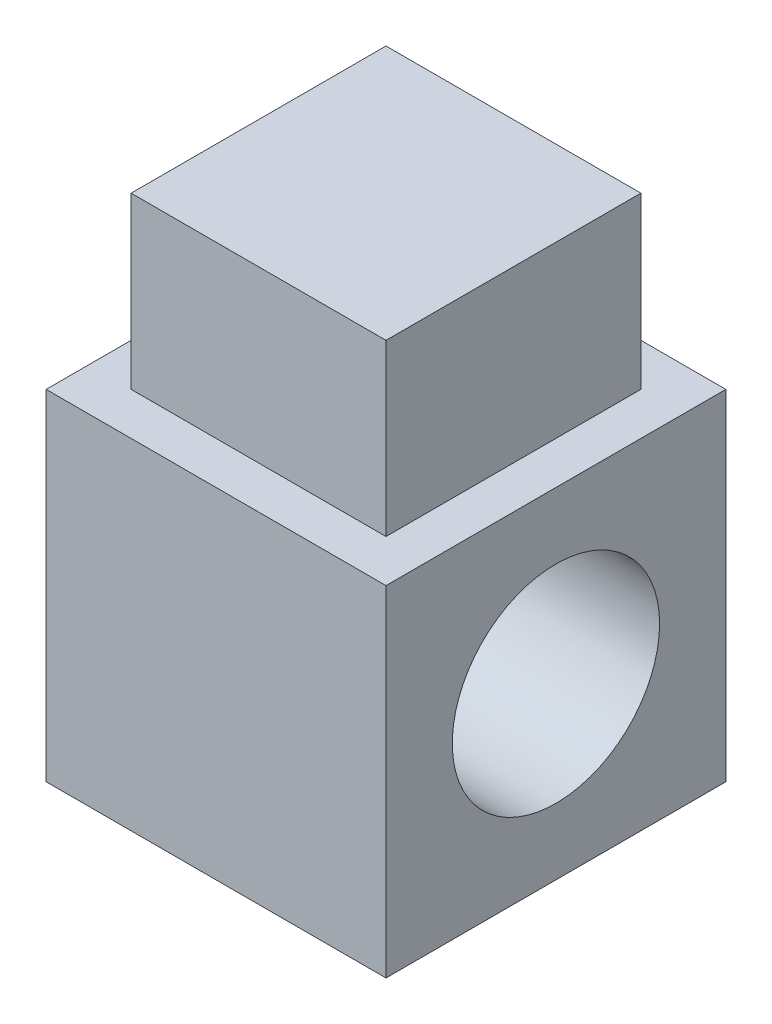
SolidWorks part; units mm, degrees
ref_plane "Front Plane" through (0, 0, 0) normal (0, 0, 1) x (1, 0, 0)
ref_plane "Top Plane" through (0, 0, 0) normal (0, 1, 0) x (1, 0, 0)
ref_plane "Right Plane" through (0, 0, 0) normal (1, 0, 0) x (0, 0, -1)
sketch "Sketch1" plane through (0, 0, 0) normal (1, 0, 0) x (0, 0, -1)
  line L1 (-10, 10) -> (10, 10)
  line L2 (-10, 10) -> (-10, -10)
  line L3 (-10, -10) -> (10, -10)
  line L4 (10, 10) -> (10, -10)
  line L5 (-10, 10) -> (10, -10) construction
  line L6 (-10, -10) -> (10, 10) construction
  circle A0 centre (0, 0) radius 6.1
  dimension "D1" = 12.2
  dimension "D2" = 20
  dimension "D3" = 20
extrude "Boss-Extrude1" add sketch "Sketch1" along normal mid plane 20
sketch "Sketch3" plane through (0, 10, 0) normal (0, 1, 0) x (1, 0, 0)
  line L1 (-7.5, 7.5) -> (7.5, 7.5)
  line L2 (-7.5, 7.5) -> (-7.5, -7.5)
  line L3 (-7.5, -7.5) -> (7.5, -7.5)
  line L4 (7.5, 7.5) -> (7.5, -7.5)
  line L5 (-7.5, 7.5) -> (7.5, -7.5) construction
  line L6 (-7.5, -7.5) -> (7.5, 7.5) construction
  point P0 (0, 0)
  dimension "D1" = 15
  dimension "D2" = 15
extrude "Boss-Extrude2" add sketch "Sketch3" along normal blind 10
